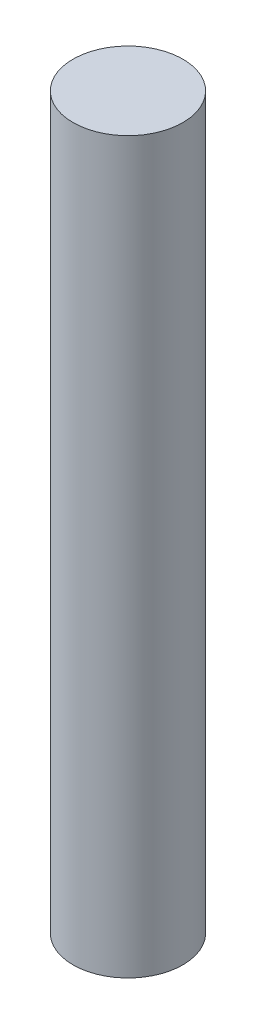
SolidWorks part; units mm, degrees
ref_plane "Front Plane" through (0, 0, 0) normal (0, 0, 1) x (1, 0, 0)
ref_plane "Top Plane" through (0, 0, 0) normal (0, 1, 0) x (1, 0, 0)
ref_plane "Right Plane" through (0, 0, 0) normal (1, 0, 0) x (0, 0, -1)
sketch "Sketch1" plane through (0, 0, 0) normal (0, 1, 0) x (1, 0, 0)
  circle A0 centre (0, 0) radius 15.875
  dimension "D1" = 31.75
extrude "Boss-Extrude1" add sketch "Sketch1" along normal blind 210.82
